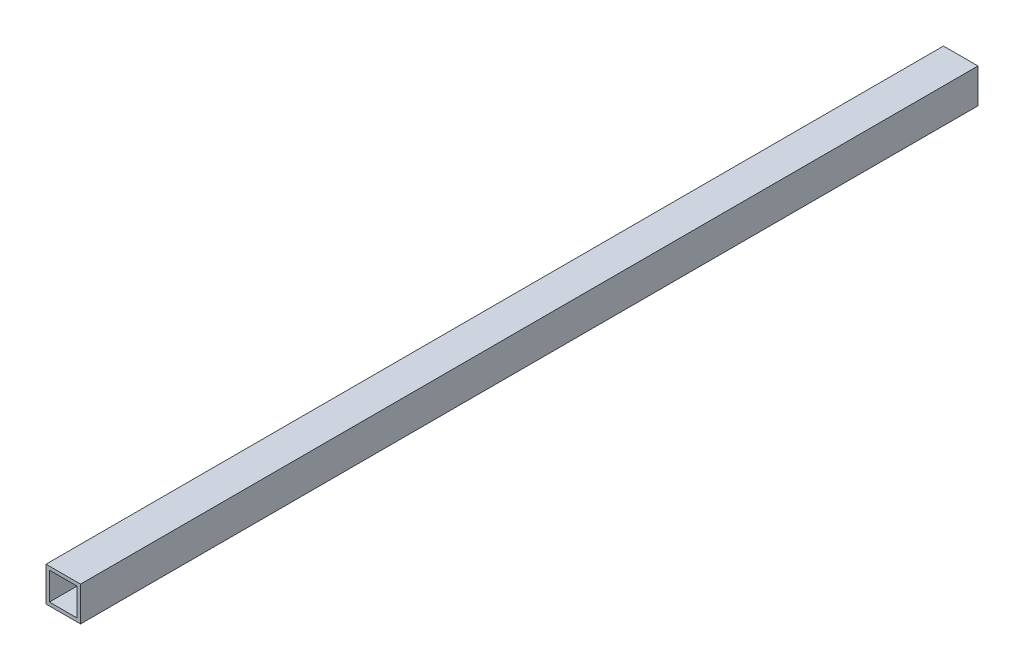
SolidWorks part; units mm, degrees
material "1.0037 (S235JR)"
ref_plane "Front Plane" through (0, 0, 0) normal (0, 0, 1) x (1, 0, 0)
ref_plane "Top Plane" through (0, 0, 0) normal (0, 1, 0) x (1, 0, 0)
ref_plane "Right Plane" through (0, 0, 0) normal (1, 0, 0) x (0, 0, -1)
curve "Curve1"
  spline degree 1 poles (0, 0, -520) (0, 0, 520) knots 0 0 1 1
sketch "Sketch1" plane through (0, 0, 0) normal (0, 0, 1) x (1, 0, 0)
  line L0 (0, 35.3535) -> (0, -33.8384) construction
  line L1 (-20, 20) -> (20, 20)
  line L2 (-20, 20) -> (-20, -20)
  line L3 (-20, -20) -> (20, -20)
  line L4 (20, 20) -> (20, -20)
  line L5 (-16, 16) -> (16, 16)
  line L6 (-16, 16) -> (-16, -16)
  line L7 (-16, -16) -> (16, -16)
  line L8 (16, 16) -> (16, -16)
  line L9 (-39.3939, 0) -> (41.5152, 0) construction
  dimension "D1" = 40
  dimension "D2" = 32
sweep "Sweep1" add profiles "Sketch1" path "Curve1"
